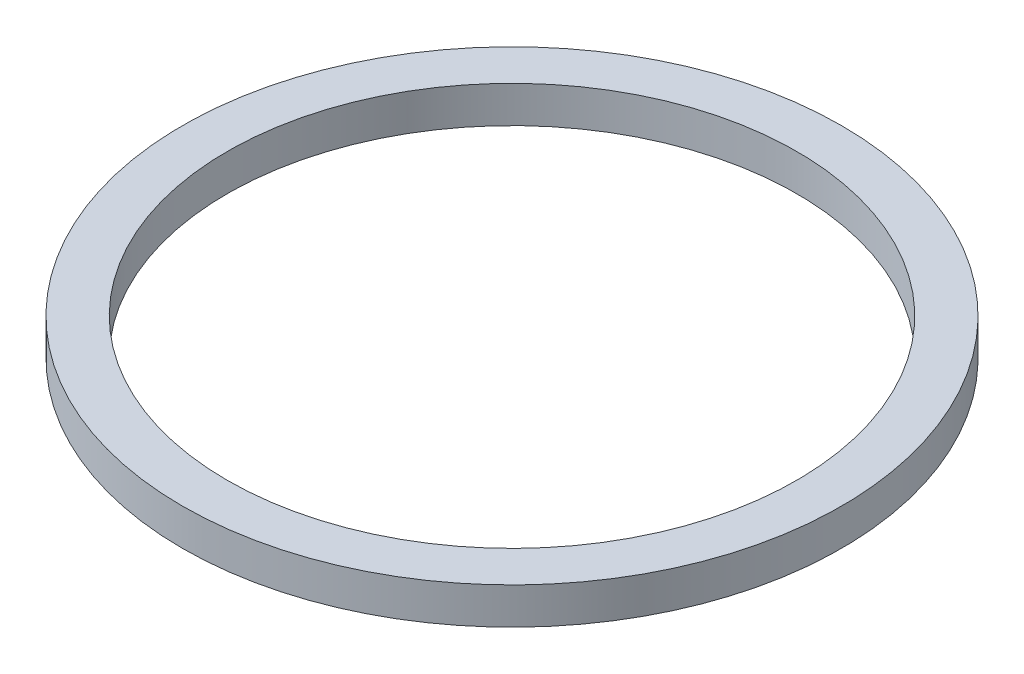
SolidWorks part; units mm, degrees
ref_plane "Front Plane" through (0, 0, 0) normal (0, 0, 1) x (1, 0, 0)
ref_plane "Top Plane" through (0, 0, 0) normal (0, 1, 0) x (1, 0, 0)
ref_plane "Right Plane" through (0, 0, 0) normal (1, 0, 0) x (0, 0, -1)
sketch "Sketch1" plane through (0, 0, 0) normal (0, 1, 0) x (1, 0, 0)
  circle A0 centre (0, 0) radius 40.5
  dimension "D1" = 81
extrude "Boss-Extrude1" add sketch "Sketch1" along normal blind 4.5
sketch "Sketch2" plane through (0, 4.5, 0) normal (0, 1, 0) x (1, 0, 0)
  circle A0 centre (0, 0) radius 35
  dimension "D1" = 70
extrude "Cut-Extrude1" cut sketch "Sketch2" against normal through all
sketch "Sketch3" plane through (0, 0, 0) normal (0, 1, 0) x (1, 0, 0)
  line L0 (0, 0) -> (-55.1114, -71.5468) construction
  line L1 (0, 0) -> (0, -112.53) construction
  line L2 (-27.2999, -23.151) -> (-73.769, -83.4782)
  line L3 (-30, -156.93) -> (30, -156.93) construction
  line L4 (-30, -156.93) -> (-30, -68.13) construction
  line L5 (-30, -68.13) -> (30, -68.13) construction
  line L6 (30, -156.93) -> (30, -68.13) construction
  line L7 (0, -68.13) -> (0, -156.93) construction
  line L8 (-30, -112.53) -> (30, -112.53) construction
  line L9 (-27.2999, -23.151) -> (-15.4166, -32.3045)
  line L10 (-73.769, -83.4782) -> (-61.8857, -92.6317)
  line L11 (-15.4166, -32.3045) -> (-61.8857, -92.6317)
  line L12 (-67.8274, -88.055) -> (-21.3582, -27.7277) construction
  line L13 (-50.5345, -53.3146) -> (-38.6512, -62.4681) construction
  line L15 (-45.2067, -68.13) -> (-33.1345, -68.13)
  line L16 (-45.2067, -68.13) -> (-45.2067, -96.7132)
  line L17 (-45.2067, -96.7132) -> (-33.1345, -96.7132)
  line L18 (-33.1345, -68.13) -> (-33.1345, -96.7132)
  line L19 (-39.1706, -96.7132) -> (-39.1706, -68.13) construction
  line L20 (-45.2067, -82.4216) -> (-33.1345, -82.4216) construction
  circle A0 centre (0, 0) radius 35 construction
  point P7 (-58.5093, -91.4435)
  point P8 (-44.5928, -57.8913)
  point P13 (-39.1706, -82.4216)
  point P17 (-67.8274, -88.055)
  dimension "D1" = 60
  dimension "D2" = 68.13
  dimension "D3" = 15
